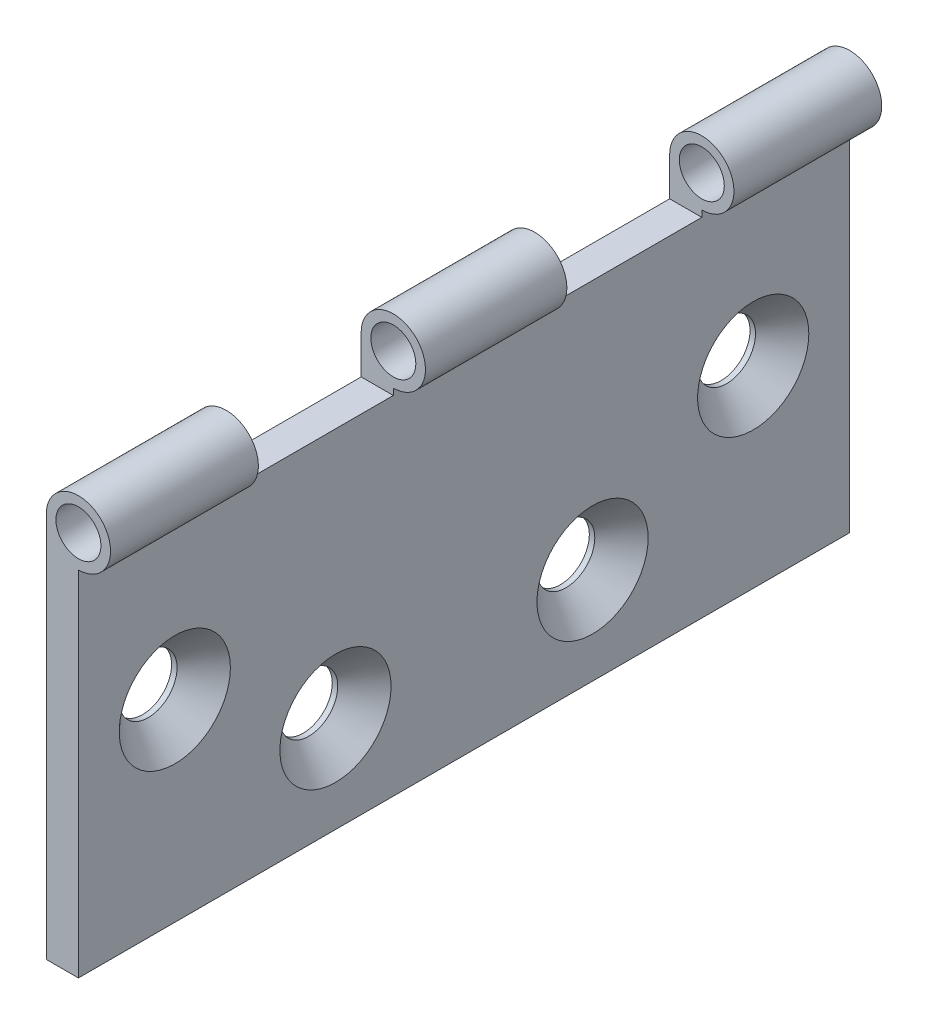
SolidWorks part; units mm, degrees
ref_plane "Front" through (0, 0, 0) normal (0, 0, 1) x (1, 0, 0)
ref_plane "Top" through (0, 0, 0) normal (0, 1, 0) x (1, 0, 0)
ref_plane "Right" through (0, 0, 0) normal (1, 0, 0) x (0, 0, -1)
sketch "Sketch15" plane through (0, 0, 0) normal (0, 0, 1) x (1, 0, 0)
  line L0 (0, 0) -> (0, 60)
  dimension "D1" = 60
extrude "Extrude-Thin2" add sketch "Sketch15" along normal mid plane 120 thin
sketch "Sketch16" plane through (0, 0, -60) normal (0, 0, -1) x (-1, 0, 0)
  circle A0 centre (-5, 60) radius 5
  dimension "D1" = 10
sweep "Sweep2" add profiles "Sketch16" path edge at (5, 60, 0)
sketch "Sketch17" plane through (0, 0, 60) normal (0, 0, 1) x (1, 0, 0)
  line L0 (0, 0) -> (0, 60) construction
  circle A0 centre (5, 60) radius 3.5
  dimension "D3" = 7
  dimension "D1" = 5
  dimension "D2" = 5
extrude "Cut-Extrude4" cut sketch "Sketch17" against normal through all
hole_wizard "CSK for M8 Flat Head Machine Screw4" positions "Sketch19" profile "Sketch18" countersink size "M8" standard "ANSI Metric" end condition through all
sketch "Sketch19" plane through (5, 0, 0) normal (1, 0, 0) x (0, 0, -1)
  line L0 (-60, 0) -> (60, 0) construction
  point P0 (-45, 30)
  point P2 (-20, 15)
  dimension "D1" = 30
  dimension "D2" = 15
  dimension "D3" = 15
  dimension "D4" = 40
sketch "Sketch18" plane through (5, 30, 45) normal (0, 1, 0) x (0, 0, -1)
  line L0 (0, 0) -> (0, 5)
  line L1 (0, 5) -> (4.5, 5)
  line L2 (4.5, 5) -> (4.5, 4.15)
  line L3 (4.5, 4.15) -> (8.65, 0)
  line L5 (8.65, 0) -> (0, 0)
  line L6 (-4.5, 4.15) -> (-8.65, 0) construction
  line L11 (0, -6.35) -> (0, 107.95) construction
  dimension "Thru Hole Dia." = 9
  dimension "Thru Hole Depth" = 5
  dimension "Near C'Sink Dia." = 17.3
  dimension "Near C'Sink Angle" = 90
mirror "Mirror7" about plane through (0, 0, 0) normal (0, 0, 1) of "CSK for M8 Flat Head Machine Screw4"
sketch "layout for cuts" plane through (5, 0, 0) normal (1, 0, 0) x (0, 0, -1)
  line L4 (60, 54) -> (-60, 54)
  line L5 (-60, 65) -> (-60, 55) construction
  line L6 (60, 55) -> (60, 65) construction
  line L7 (-60, 65) -> (-60, 54)
  line L8 (60, 0) -> (60, 55)
  line L9 (60, 55) -> (-60, 55)
  line L10 (-60, 55) -> (-60, 0)
  line L11 (-60, 0) -> (60, 0)
  line L12 (60, 0) -> (60, 55)
  line L13 (60, 55) -> (-60, 55)
  line L14 (-60, 55) -> (-60, 0)
  line L15 (-60, 0) -> (60, 0)
  line L16 (60, 54) -> (60, 65)
  line L17 (-60, 65) -> (60, 65)
  line L18 (-36, 65) -> (-36, 54)
  line L19 (-12, 65) -> (-12, 54)
  line L20 (36, 65) -> (36, 54)
  line L21 (12, 65) -> (12, 54)
  dimension "D3" = 24
  dimension "D4" = 24
  dimension "D5" = 24
  dimension "D6" = 24
  dimension "D1" = 0
  dimension "D2" = 1
sketch "Sketch37" plane through (5, 0, 0) normal (1, 0, 0) x (0, 0, -1)
  line L0 (60, 54) -> (-60, 54) construction
  line L2 (-60, 65) -> (60, 65) construction
  line L4 (37, 54) -> (11, 54)
  line L5 (-11, 54) -> (-37, 54)
  line L6 (-37, 65) -> (-11, 65)
  line L10 (-37, 65) -> (-37, 54)
  line L11 (-37, 65) -> (-37, 54)
  line L13 (37, 65) -> (37, 54)
  line L14 (37, 65) -> (37, 54)
  line L16 (-11, 65) -> (-11, 54)
  line L17 (-11, 65) -> (-11, 54)
  line L18 (11, 65) -> (37, 65)
  line L19 (11, 65) -> (11, 54)
  line L20 (11, 65) -> (11, 54)
  dimension "D1" = 1
  dimension "D2" = 1
  dimension "D3" = 1
  dimension "D4" = 1
extrude "2Cuts" cut sketch "Sketch37" against normal through all and the other way through all
sketch "Sketch35" plane through (5, 0, 0) normal (1, 0, 0) x (0, 0, -1)
  line L0 (60, 54) -> (-60, 54) construction
  line L1 (-60, 65) -> (-60, 54) construction
  line L2 (-60, 65) -> (60, 65) construction
  line L3 (60, 54) -> (60, 65) construction
  line L12 (60, 54) -> (35, 54)
  line L13 (-60, 65) -> (-60, 54)
  line L14 (-60, 65) -> (-35, 65)
  line L15 (60, 54) -> (60, 65)
  line L18 (-35, 65) -> (-35, 54)
  line L19 (-35, 65) -> (-35, 54)
  line L21 (-11, 65) -> (-11, 54)
  line L22 (-11, 65) -> (-11, 54)
  line L24 (11, 65) -> (11, 54)
  line L25 (11, 65) -> (11, 54)
  line L26 (-11, 65) -> (11, 65)
  line L27 (35, 65) -> (35, 54)
  line L28 (35, 65) -> (35, 54)
  line L29 (-35, 54) -> (-60, 54)
  line L30 (11, 54) -> (-11, 54)
  line L31 (35, 65) -> (60, 65)
  dimension "D2" = 1
  dimension "D3" = 1
  dimension "D4" = 1
  dimension "D5" = 1
extrude "3Cuts" [suppressed] cut sketch "Sketch35" against normal through all and the other way through all
